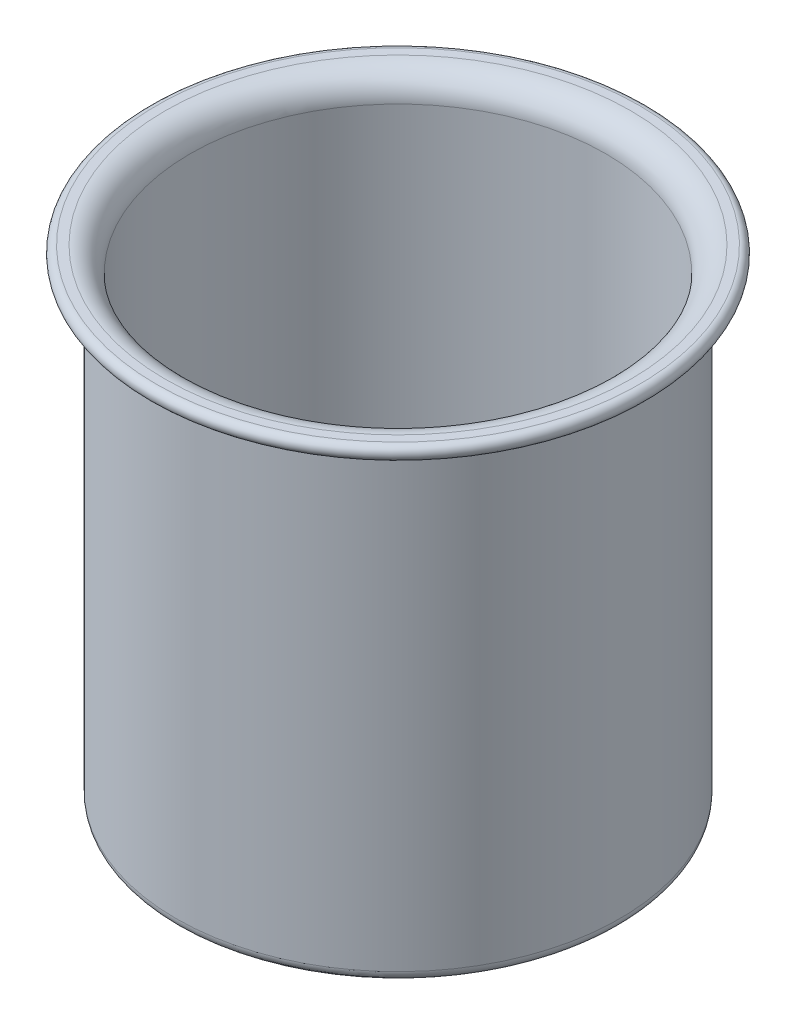
SolidWorks part; units mm, degrees
ref_plane "Front Plane" through (0, 0, 0) normal (0, 0, 1) x (1, 0, 0)
ref_plane "Top Plane" through (0, 0, 0) normal (0, 1, 0) x (1, 0, 0)
ref_plane "Right Plane" through (0, 0, 0) normal (1, 0, 0) x (0, 0, -1)
sketch "Sketch1" plane through (0, 0, 0) normal (0, 0, 1) x (1, 0, 0)
  line L0 (0, 0) -> (0, 136.6969) construction
  line L1 (0, 0) -> (-59.5, 0)
  line L2 (-62.5, 3) -> (-62.5, 129)
  line L3 (-65.5, 132) -> (-67.9836, 132)
  line L4 (0, 4) -> (-58.5, 4)
  line L5 (-58.5, 4) -> (-58.5, 129)
  line L6 (-65.5, 136) -> (-67.9836, 136)
  line L7 (0, 4) -> (0, 0)
  arc A0 (-62.5, 129) -> (-65.5, 132) centre (-65.5, 129) ccw
  arc A1 (-59.5, 0) -> (-62.5, 3) centre (-59.5, 3) cw
  arc A2 (-58.5, 4) -> (-58.5, 4) centre (-58.5, 4) cw
  arc A3 (-58.5, 129) -> (-65.5, 136) centre (-65.5, 129) ccw
  arc A4 (-67.9836, 136) -> (-67.9836, 132) centre (-67.9836, 134) ccw
  point P10 (-66.7418, 132)
  dimension "D1" = 3
  dimension "D2" = 62.5
  dimension "D3" = 132
  dimension "D4" = 4
revolve "Revolve1" add sketch "Sketch1" angle 360 about L0
